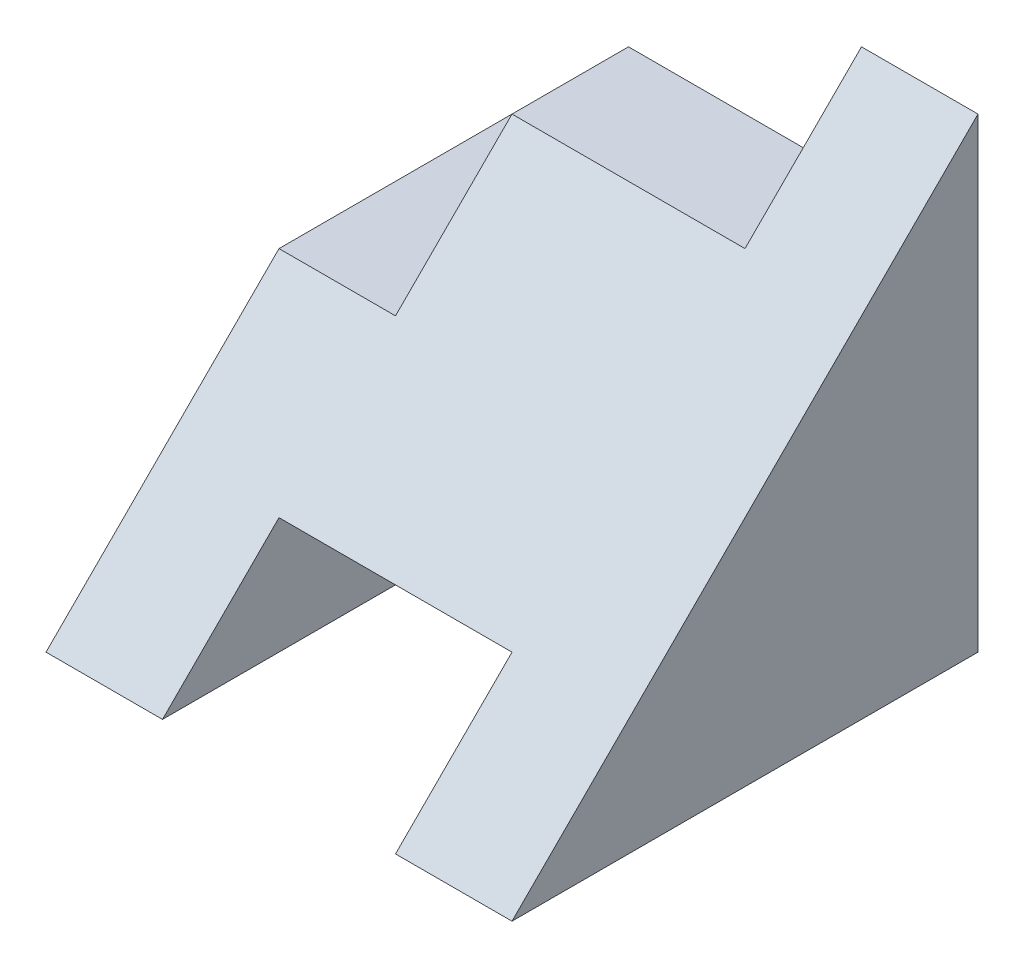
SolidWorks part; units mm, degrees
ref_plane "Front" through (0, 0, 0) normal (0, 0, 1) x (1, 0, 0)
ref_plane "Top" through (0, 0, 0) normal (0, 1, 0) x (1, 0, 0)
ref_plane "Right" through (0, 0, 0) normal (1, 0, 0) x (0, 0, -1)
sketch "Sketch1" plane through (0, 0, 0) normal (0, 0, 1) x (1, 0, 0)
  line L0 (0, 0) -> (0, 2)
  line L1 (0, 2) -> (1, 2)
  line L2 (1, 2) -> (1, 3)
  line L3 (1, 3) -> (3, 3)
  line L4 (3, 3) -> (3, 4)
  line L5 (3, 4) -> (4, 4)
  line L6 (4, 4) -> (4, 0)
  line L7 (4, 0) -> (3, 0)
  line L8 (3, 0) -> (3, 1)
  line L9 (3, 1) -> (1, 1)
  line L10 (1, 1) -> (1, 0)
  line L11 (1, 0) -> (0, 0)
  dimension "D1" = 4
  dimension "D2" = 1
  dimension "D3" = 1
  dimension "D4" = 1
  dimension "D5" = 1
  dimension "D6" = 2
  dimension "D7" = 1
  dimension "D8" = 1
  dimension "D9" = 2
extrude "Boss-Extrude1" add sketch "Sketch1" along normal blind 4
sketch "Sketch3" plane through (0, 0, 0) normal (-1, 0, 0) x (0, 0, 1)
  line L0 (4, 0) -> (0, 4)
  line L1 (0, 4) -> (4, 4)
  line L2 (4, 4) -> (4, 0)
extrude "Cut-Extrude2" cut sketch "Sketch3" against normal blind 10
